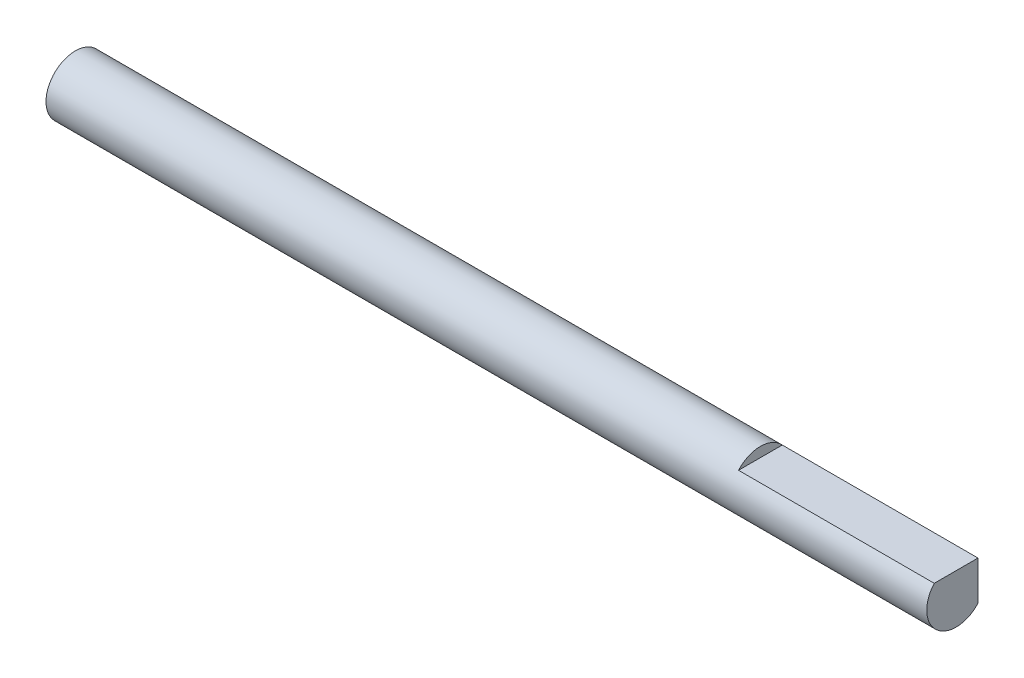
SolidWorks part; units mm, degrees
material "Brass"
ref_plane "Front" through (0, 0, 0) normal (0, 0, 1) x (1, 0, 0)
ref_plane "Top" through (0, 0, 0) normal (0, 1, 0) x (1, 0, 0)
ref_plane "Right" through (0, 0, 0) normal (1, 0, 0) x (0, 0, -1)
sketch "Sketch1" plane through (0, 0, 0) normal (1, 0, 0) x (0, 0, -1)
  circle A0 centre (0, 0) radius 1.5
  dimension "D1" = 3
extrude "Boss-Extrude1" add sketch "Sketch1" along normal mid plane 45
sketch "Sketch2" plane through (22.5, 0, 0) normal (1, 0, 0) x (0, 0, -1)
  line L0 (1.118, 1) -> (-1.118, 1)
  arc A0 (-1.118, 1) -> (1.118, 1) centre (0, 0) cw
  circle A1 centre (0, 0) radius 1.5 construction
  dimension "D1" = 1
extrude "Cut-Extrude1" cut sketch "Sketch2" against normal blind 10
sketch "Sketch3" plane through (22.5, 0, 0) normal (1, 0, 0) x (0, 0, -1)
  line L0 (1.118, 1) -> (1.118, -1)
  arc A0 (-1.118, 1) -> (1.118, 1) centre (0, 0) ccw construction
  arc A1 (1.118, 1) -> (1.118, -1) centre (0, 0) cw
extrude "Cut-Extrude2" cut sketch "Sketch3" against normal up to surface (10 mm away) up to face at (12.5, 1.25, 0)
